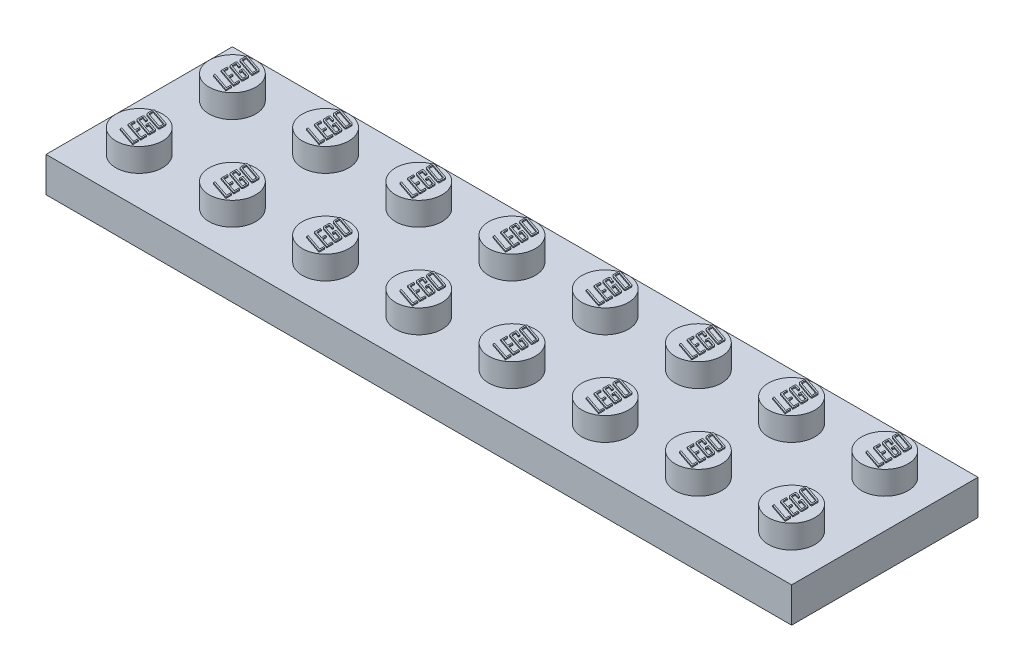
SolidWorks part; units mm, degrees
material "ABS"
ref_plane "Front Plane" through (0, 0, 0) normal (0, 0, 1) x (1, 0, 0)
ref_plane "Top Plane" through (0, 0, 0) normal (0, 1, 0) x (1, 0, 0)
ref_plane "Right Plane" through (0, 0, 0) normal (1, 0, 0) x (0, 0, -1)
sketch "Sketch1" plane through (0, 0, 0) normal (0, 1, 0) x (1, 0, 0)
  line L1 (32, -8) -> (-32, -8)
  line L2 (32, -8) -> (32, 8)
  line L3 (32, 8) -> (-32, 8)
  line L4 (-32, -8) -> (-32, 8)
  line L5 (32, -8) -> (-32, 8) construction
  line L6 (32, 8) -> (-32, -8) construction
  point P0 (0, 0)
  dimension "D1" = 64
  dimension "D2" = 16
extrude "Boss-Extrude1" add sketch "Sketch1" along normal blind 3
sketch "Sketch2" plane through (0, 3, 0) normal (0, 1, 0) x (1, 0, 0)
  line L0 (-32, 8) -> (-32, -8) construction
  line L1 (32, 8) -> (-32, 8) construction
  circle A0 centre (-28, 4) radius 2
  circle A1 centre (-20, 4) radius 2
  circle A2 centre (-12, 4) radius 2
  circle A3 centre (-4, 4) radius 2
  circle A4 centre (4, 4) radius 2
  circle A5 centre (12, 4) radius 2
  circle A6 centre (20, 4) radius 2
  circle A7 centre (28, 4) radius 2
  circle A8 centre (-20, -4) radius 2
  circle A9 centre (-12, -4) radius 2
  circle A10 centre (-4, -4) radius 2
  circle A11 centre (4, -4) radius 2
  circle A12 centre (12, -4) radius 2
  circle A13 centre (20, -4) radius 2
  circle A14 centre (28, -4) radius 2
  circle A15 centre (-28, -4) radius 2
  dimension "D1" = 4
  dimension "D2" = 4
  dimension "D3" = 4
  dimension "D4" = 8
  dimension "D5" = 2
extrude "Boss-Extrude2" add sketch "Sketch2" along normal blind 2
shell "Shell1" thickness 1
sketch "Sketch3" plane through (0, 2, 0) normal (0, -1, 0) x (1, 0, 0)
  line L0 (-32, -8) -> (-32, 8) construction
  circle A0 centre (-24, 0) radius 2.8
  circle A1 centre (-24, 0) radius 1.8
  dimension "D1" = 5.6
  dimension "D2" = 3.6
  dimension "D3" = 8
extrude "Boss-Extrude3" add sketch "Sketch3" along normal blind 2
pattern_linear "LPattern1" count 7 spacing 8 along (1, 0, 0) of "Boss-Extrude3"
sketch "Sketch4" plane through (0, 5, 0) normal (0, 1, 0) x (1, 0, 0)
  line L0 (-28, -6) -> (-28, -2) construction
  line L1 (-28, -2) -> (-27, -2) construction
  line L2 (-27, -2) -> (-27, -5.7) construction
  circle A0 centre (-28, -4) radius 2 construction
  circle A1 centre (-28, -4) radius 2 construction
  text T0 "<i>LEGO</i>" font "Agency FB" height in points 6
  dimension "D1" = 1
  dimension "D2" = 3.7
extrude "Boss-Extrude4" add sketch "Sketch4" along normal blind 0.1
pattern_linear "LPattern2" count 8 spacing 8 along (1, 0, 0) count 2 spacing 8 along (0, 0, 1) of "Boss-Extrude4"
